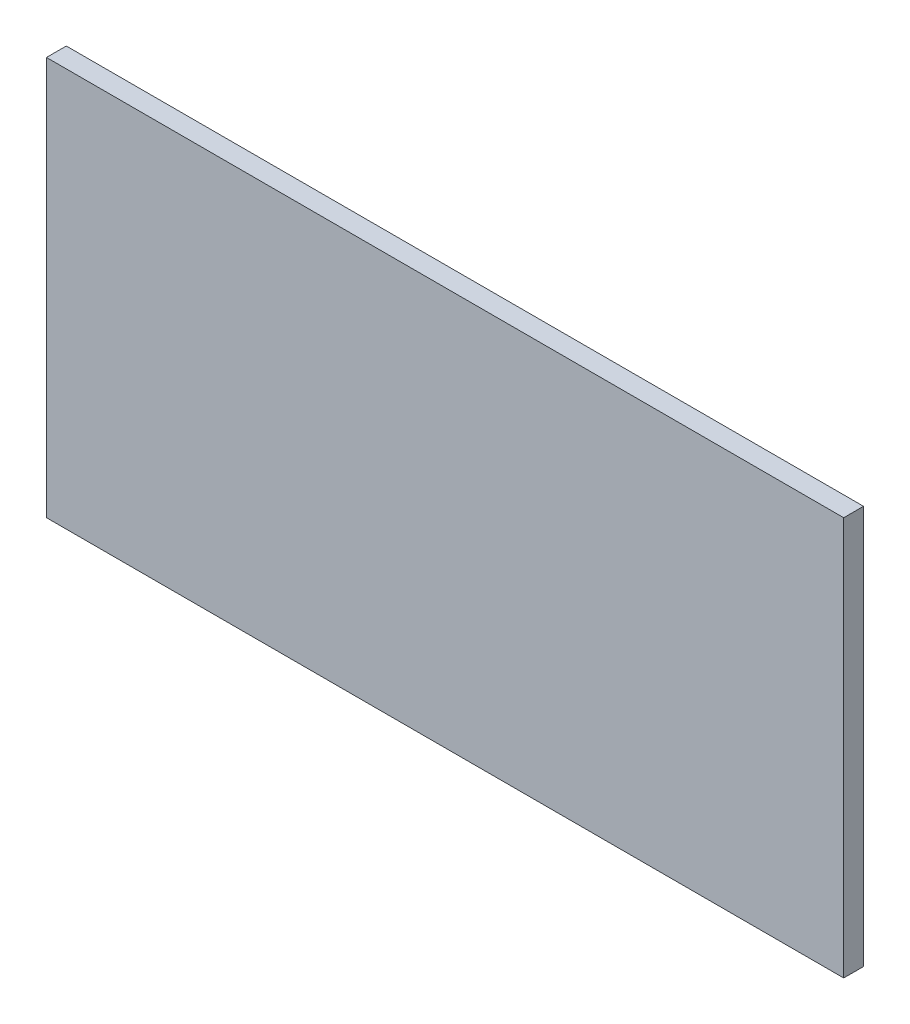
SolidWorks part; units mm, degrees
material "Black Acrylic"
ref_plane "Front Plane" through (0, 0, 0) normal (0, 0, 1) x (1, 0, 0)
ref_plane "Top Plane" through (0, 0, 0) normal (0, 1, 0) x (1, 0, 0)
ref_plane "Right Plane" through (0, 0, 0) normal (1, 0, 0) x (0, 0, -1)
sketch "Sketch1" plane through (0, 0, 0) normal (0, 0, 1) x (1, 0, 0)
  line L0 (-90.5, 0) -> (-90.5, -90.5)
  line L1 (-90.5, -90.5) -> (90.5, -90.5)
  line L2 (90.5, -90.5) -> (90.5, 0)
  line L3 (90.5, 0) -> (-90.5, 0)
  line L4 (90.5, -90.5) -> (-90.5, 90.5) construction
  line L5 (-90.5, -90.5) -> (90.5, 90.5) construction
  line L6 (90.5, -90.5) -> (90.5, 90.5) construction
  point P4 (0, 0)
  dimension "D1" = 181
  dimension "D2" = 181
extrude "Boss-Extrude1" add sketch "Sketch1" along normal mid plane 4.5
